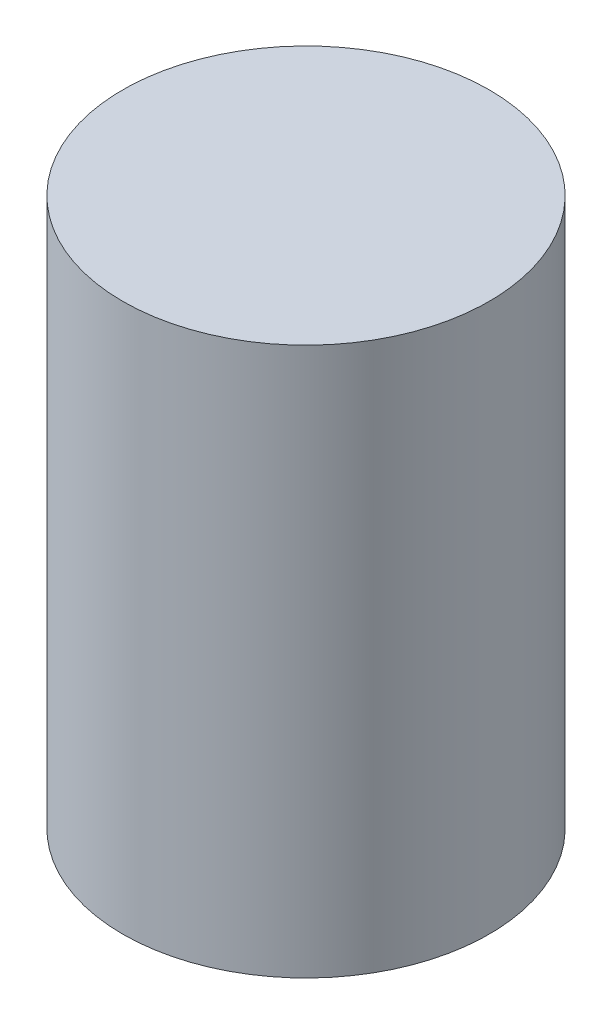
SolidWorks part; units mm, degrees
ref_plane "Front" through (0, 0, 0) normal (0, 0, 1) x (1, 0, 0)
ref_plane "Top" through (0, 0, 0) normal (0, 1, 0) x (1, 0, 0)
ref_plane "Right" through (0, 0, 0) normal (1, 0, 0) x (0, 0, -1)
sketch "Sketch1" plane through (0, 0, 0) normal (0, 1, 0) x (1, 0, 0)
  circle A0 centre (0, 0) radius 22.2504
  dimension "D1" = 44.5008
extrude "Boss-Extrude1" add sketch "Sketch1" along normal blind 66.548
